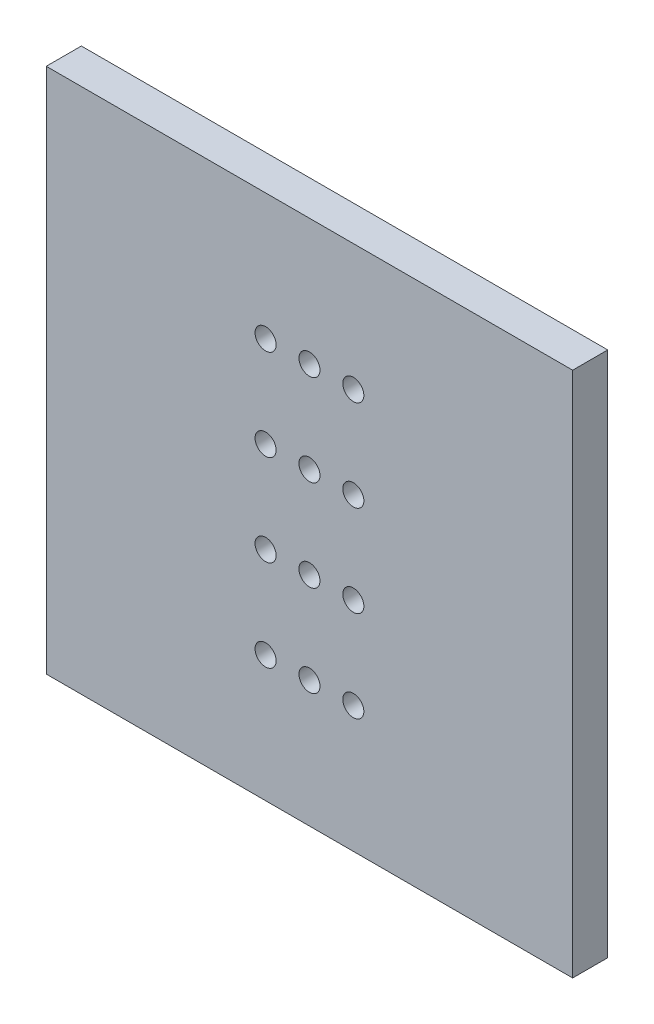
SolidWorks part; units mm, degrees
ref_plane "Plan de face" through (0, 0, 0) normal (0, 0, 1) x (1, 0, 0)
ref_plane "Plan de dessus" through (0, 0, 0) normal (0, 1, 0) x (1, 0, 0)
ref_plane "Plan de droite" through (0, 0, 0) normal (1, 0, 0) x (0, 0, -1)
sketch "Esquisse1" plane through (0, 0, 0) normal (0, 0, 1) x (1, 0, 0)
  line L1 (-15, -15) -> (15, -15)
  line L2 (-15, -15) -> (-15, 15)
  line L3 (-15, 15) -> (15, 15)
  line L4 (15, -15) -> (15, 15)
  line L5 (-15, -15) -> (15, 15) construction
  line L6 (-15, 15) -> (15, -15) construction
  point P0 (0, 0)
extrude "Base_Plate" add sketch "Esquisse1" along normal blind 2
sketch "Sketch_Perforations" plane through (0, 0, 2) normal (0, 0, 1) x (1, 0, 0)
  circle A0 centre (-2.5, -7.8) radius 0.6
  circle A1 centre (-2.5, -2.6) radius 0.6
  circle A2 centre (-2.5, 2.6) radius 0.6
  circle A3 centre (-2.5, 7.8) radius 0.6
  circle A4 centre (0, -7.8) radius 0.6
  circle A5 centre (0, -2.6) radius 0.6
  circle A6 centre (0, 2.6) radius 0.6
  circle A7 centre (0, 7.8) radius 0.6
  circle A8 centre (2.5, -7.8) radius 0.6
  circle A9 centre (2.5, -2.6) radius 0.6
  circle A10 centre (2.5, 2.6) radius 0.6
  circle A11 centre (2.5, 7.8) radius 0.6
extrude "Cut_Perforations" cut sketch "Sketch_Perforations" against normal blind 10
